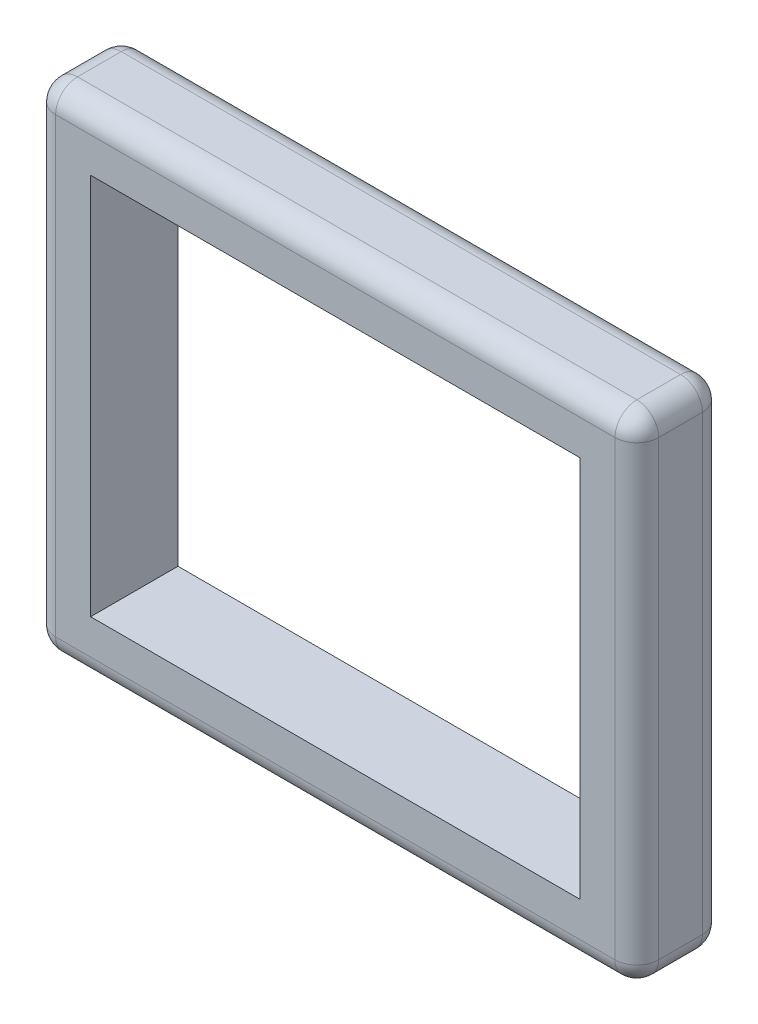
SolidWorks part; units mm, degrees
ref_plane "Front Plane" through (0, 0, 0) normal (0, 0, 1) x (1, 0, 0)
ref_plane "Top Plane" through (0, 0, 0) normal (0, 1, 0) x (1, 0, 0)
ref_plane "Right Plane" through (0, 0, 0) normal (1, 0, 0) x (0, 0, -1)
sketch "Sketch1" plane through (0, 0, 0) normal (0, 0, 1) x (1, 0, 0)
  line L1 (0, 0) -> (711.2, 0)
  line L2 (0, 0) -> (0, 555.625)
  line L3 (0, 555.625) -> (711.2, 555.625)
  line L4 (711.2, 0) -> (711.2, 555.625)
  line L6 (0, 0) -> (0, 161.9753)
  line L9 (-82.55, 638.175) -> (793.75, 638.175)
  line L10 (-82.55, 638.175) -> (-82.55, -82.55)
  line L11 (-82.55, -82.55) -> (793.75, -82.55)
  line L12 (793.75, 638.175) -> (793.75, -82.55)
  dimension "D1" = 711.2
  dimension "D2" = 555.625
  dimension "D3" = 82.55
  dimension "D4" = 82.55
  dimension "D5" = 82.55
  dimension "D6" = 82.55
extrude "Boss-Extrude1" add sketch "Sketch1" along normal blind 127 contours L12 L9 L10 L11 L4 L1 L2 L3
fillet "Fillet1" radius 31.75 12 edges at (355.6, 638.175, 0) (355.6, 638.175, 127) (793.75, 277.8125, 0) (793.75, 277.8125, 127) (355.6, -82.55, 0) (355.6, -82.55, 127) (-82.55, 277.8125, 0) (-82.55, 277.8125, 127) (-82.55, 638.175, 63.5) (793.75, 638.175, 63.5) (793.75, -82.55, 63.5) (-82.55, -82.55, 63.5)
